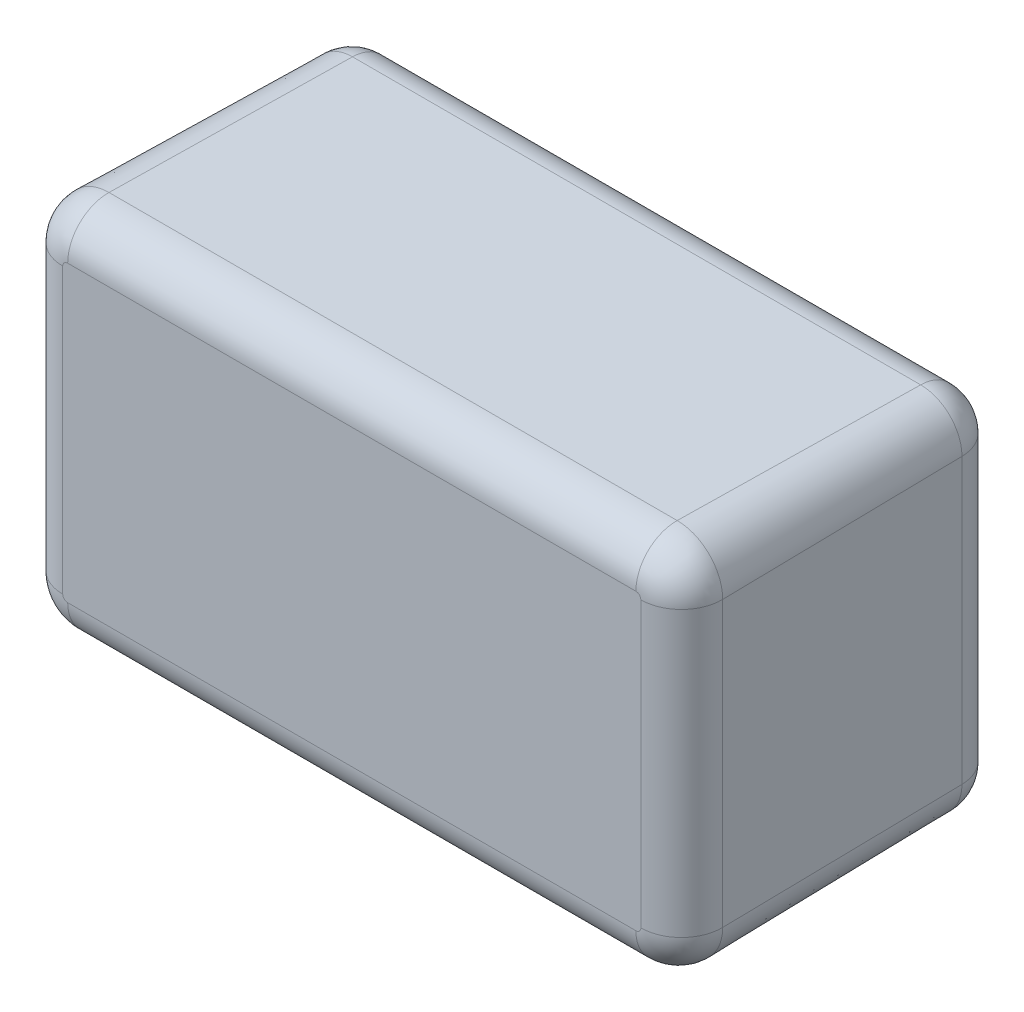
SolidWorks part; units mm, degrees
ref_plane "Front Plane" through (0, 0, 0) normal (0, 0, 1) x (1, 0, 0)
ref_plane "Top Plane" through (0, 0, 0) normal (0, 1, 0) x (1, 0, 0)
ref_plane "Right Plane" through (0, 0, 0) normal (1, 0, 0) x (0, 0, -1)
sketch "Sketch1" plane through (0, 0, 0) normal (0, 0, 1) x (1, 0, 0)
  line L1 (-70, 45) -> (70, 45)
  line L2 (-80, 35) -> (-80, -35)
  line L3 (-70, -45) -> (70, -45)
  line L4 (80, 35) -> (80, -35)
  line L5 (-80, 45) -> (80, -45) construction
  line L6 (-80, -45) -> (80, 45) construction
  arc A0 (-70, 45) -> (-80, 35) centre (-70, 35) ccw
  arc A1 (-80, -35) -> (-70, -45) centre (-70, -35) ccw
  arc A2 (70, -45) -> (80, -35) centre (70, -35) ccw
  arc A3 (70, 45) -> (80, 35) centre (70, 35) cw
  point P0 (0, 0)
  dimension "D1" = 10
  dimension "D2" = 160
  dimension "D3" = 90
extrude "Boss-Extrude1" add sketch "Sketch1" along normal blind 80
draft "Draft1" type of draft neutral plane draft angle 1 faces to draft 8 face at (-76.0355, -41.0355, 40) face at (-76.0355, 41.0355, 40) face at (76.0355, 41.0355, 40) face at (76.0355, -41.0355, 40) face at (80, 0, 40) face at (0, -45, 40) face at (-80, 0, 40) face at (0, 45, 40) neutral plane through (-70, 35, 0) neutral plane normal (0, 0, -1) parameters "D1"=1
fillet "Fillet1" radius 10 16 edges at (-77.0711, 42.0711, 0) (-80, 0, 0) (-77.0711, -42.0711, 0) (0, -45, 0) (77.0711, -42.0711, 0) (80, 0, 0) (77.0711, 42.0711, 0) (0, 45, 0) (78.0585, 43.0585, 80) (81.3964, 0, 80) (78.0585, -43.0585, 80) (0, -46.3964, 80) (-78.0585, -43.0585, 80) (-81.3964, 0, 80) (-78.0585, 43.0585, 80) (0, 46.3964, 80)
shell "Shell2" thickness 2.5
